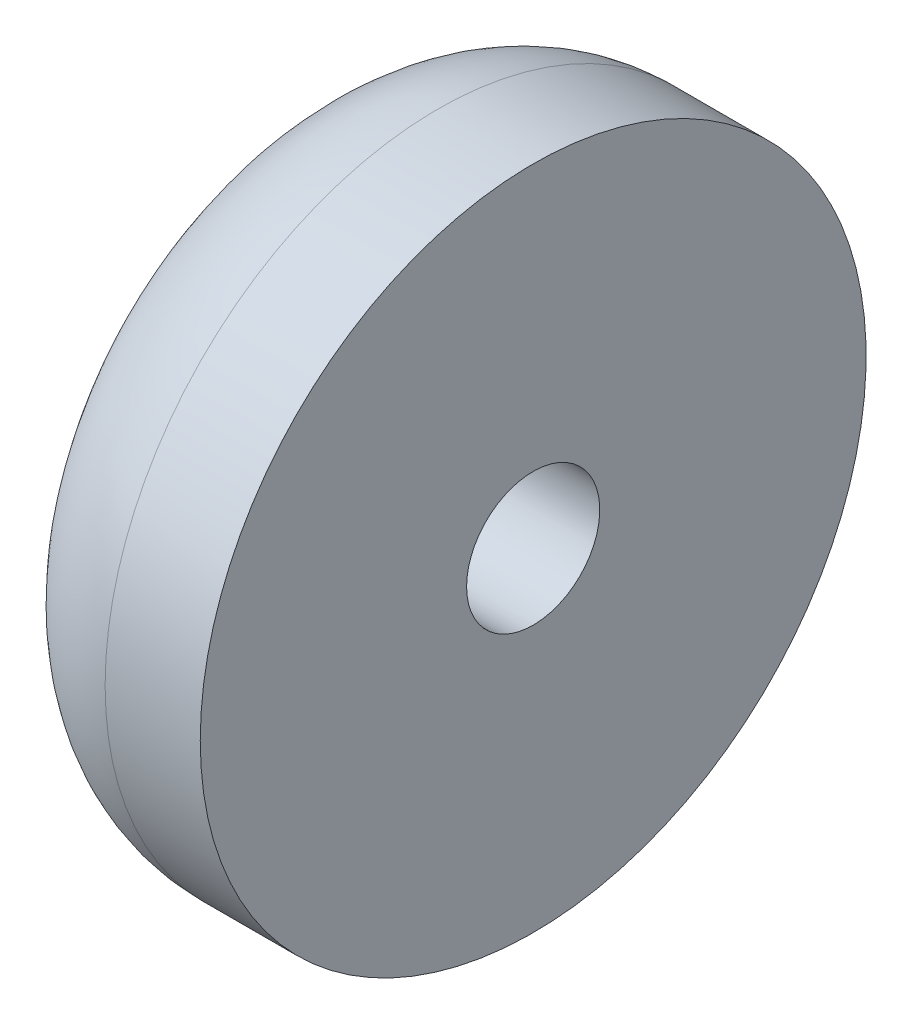
SolidWorks part; units mm, degrees
ref_plane "Alzado" through (0, 0, 0) normal (0, 0, 1) x (1, 0, 0)
ref_plane "Planta" through (0, 0, 0) normal (0, 1, 0) x (1, 0, 0)
ref_plane "Vista lateral" through (0, 0, 0) normal (1, 0, 0) x (0, 0, -1)
sketch "Croquis5" plane through (-29.1696, 0, 0) normal (-1, 0, 0) x (0, 0, 1)
  circle A4 centre (65.25, 31.0637) radius 7
  circle A6 centre (65.25, 31.0637) radius 3.65
  circle A8 centre (65.25, 31.0637) radius 3.65
  dimension "D2" = 14
  dimension "D1" = 0.15
sketch "Croquis6" plane through (-29.1696, 0, 0) normal (-1, 0, 0) x (0, 0, 1)
  circle A0 centre (65.25, 31.0637) radius 1.4 construction
  circle A2 centre (65.25, 31.0637) radius 1.4
  circle A3 centre (65.25, 31.0637) radius 7
  dimension "D1" = 14
extrude "Saliente-Extruir4" add sketch "Croquis6" along normal blind 5
fillet "Redondeo2" radius 3 1 edges at (-34.1696, 31.0637, 72.25)
sketch "Croquis7" plane through (-34.1696, 0, 0) normal (-1, 0, 0) x (0, 0, 1)
  circle A0 centre (65.25, 31.0637) radius 3
  dimension "D1" = 6
extrude "Cortar-Extruir2" cut sketch "Croquis7" against normal blind 3
